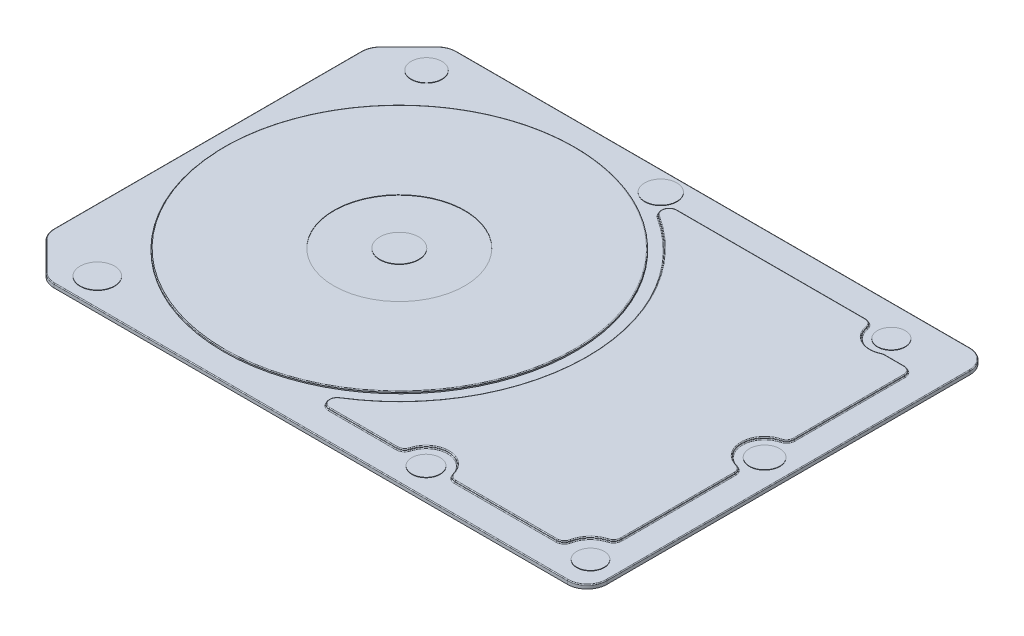
SolidWorks part; units mm, degrees
ref_plane "Front Plane" through (0, 0, 0) normal (0, 0, 1) x (1, 0, 0)
ref_plane "Top Plane" through (0, 0, 0) normal (0, 1, 0) x (1, 0, 0)
ref_plane "Right Plane" through (0, 0, 0) normal (1, 0, 0) x (0, 0, -1)
sketch "Sketch1" plane through (0, 0, 0) normal (0, 1, 0) x (1, 0, 0)
  line L0 (-72.0305, 42.3895) -> (-64.9595, 49.4605)
  line L1 (-61.4239, -50.925) -> (68.495, -50.925)
  line L2 (-73.495, -38.8539) -> (-73.495, 38.8539)
  line L3 (-61.4239, 50.925) -> (68.495, 50.925)
  line L4 (73.495, -45.925) -> (73.495, 45.925)
  line L5 (-73.495, -50.925) -> (73.495, 50.925) construction
  line L6 (-73.495, 50.925) -> (73.495, -50.925) construction
  line L7 (-72.0305, -42.3895) -> (-64.9595, -49.4605)
  arc A0 (-64.9595, -49.4605) -> (-61.4239, -50.925) centre (-61.4239, -45.925) ccw
  arc A1 (-72.0305, -42.3895) -> (-73.495, -38.8539) centre (-68.495, -38.8539) cw
  arc A2 (-72.0305, 42.3895) -> (-73.495, 38.8539) centre (-68.495, 38.8539) ccw
  arc A3 (-64.9595, 49.4605) -> (-61.4239, 50.925) centre (-61.4239, 45.925) cw
  arc A4 (68.495, -50.925) -> (73.495, -45.925) centre (68.495, -45.925) ccw
  arc A5 (68.495, 50.925) -> (73.495, 45.925) centre (68.495, 45.925) cw
  point P0 (0, 0)
  point P12 (-63.495, -50.925)
  point P15 (-73.495, -40.925)
  point P18 (-73.495, 40.925)
  point P21 (-63.495, 50.925)
  dimension "D3" = 5
  dimension "D1" = 146.99
  dimension "D2" = 101.85
extrude "cover base" add sketch "Sketch1" along normal blind 1
fillet "Fillet1" radius 0.2 12 edges at (-68.495, 1, 45.925) (-73.1144, 1, 40.7673) (-73.495, 1, 0) (-73.1144, 1, -40.7673) (-68.495, 1, -45.925) (-63.3373, 1, -50.5444) (3.5355, 1, -50.925) (72.0305, 1, -49.4605) (73.495, 1, 0) (72.0305, 1, 49.4605) (3.5355, 1, 50.925) (-63.3373, 1, 50.5444)
sketch "Sketch2" plane through (0, 1, 0) normal (0, 1, 0) x (1, 0, 0)
  circle A0 centre (-25, 0) radius 44.45
  dimension "D1" = 88.9
  dimension "D2" = 25
extrude "disk bulb" add sketch "Sketch2" along normal blind 0.5
fillet "Fillet2" radius 0.2 1 edges at (-25, 1.5, 44.45)
sketch "Sketch3" plane through (0, 1, 0) normal (0, 1, 0) x (1, 0, 0)
  line L0 (1.2049, -43.9217) -> (18.317, -43.9217)
  line L1 (33.0626, -43.9217) -> (58.7331, -43.9217)
  line L2 (66.696, -35.4916) -> (66.696, -6.7511)
  line L3 (66.696, 8.2828) -> (66.696, 36.1518)
  line L4 (64.696, 38.1518) -> (59.7928, 38.1518)
  line L5 (1.7404, 43.5821) -> (49.4372, 43.5821)
  arc A0 (0.6587, 39.8999) -> (0.1448, -40.2258) centre (-25, 0) cw
  arc A1 (51.4077, 41.9243) -> (58.9537, 37.9673) centre (56.7002, 42.8434) ccw
  arc A2 (65.2102, 6.35) -> (65.2102, -4.8184) centre (66.696, 0.7658) ccw
  arc A3 (60.6926, -42.3223) -> (65.243, -37.4153) centre (67.005, -43.6127) cw
  arc A4 (20.2473, -42.4453) -> (31.1323, -42.4453) centre (25.6898, -43.9217) cw
  arc A5 (49.4372, 43.5821) -> (51.4077, 41.9243) centre (49.4372, 41.5821) cw
  arc A6 (59.7928, 38.1518) -> (58.9537, 37.9673) centre (59.7928, 36.1518) ccw
  arc A7 (66.696, 36.1518) -> (64.696, 38.1518) centre (64.696, 36.1518) ccw
  arc A8 (66.696, 8.2828) -> (65.2102, 6.35) centre (64.696, 8.2828) cw
  arc A9 (66.696, -6.7511) -> (65.2102, -4.8184) centre (64.696, -6.7511) ccw
  arc A10 (66.696, -35.4916) -> (65.243, -37.4153) centre (64.696, -35.4916) cw
  arc A11 (58.7331, -43.9217) -> (60.6926, -42.3223) centre (58.7331, -41.9217) ccw
  arc A12 (33.0626, -43.9217) -> (31.1323, -42.4453) centre (33.0626, -41.9217) cw
  arc A13 (18.317, -43.9217) -> (20.2473, -42.4453) centre (18.317, -41.9217) ccw
  arc A14 (0.1448, -40.2258) -> (1.2049, -43.9217) centre (1.2049, -41.9217) ccw
  arc A15 (0.6587, 39.8999) -> (1.7404, 43.5821) centre (1.7404, 41.5821) cw
  point P0 (-25, 0)
  point P28 (66.696, -5.0126)
  point P37 (20.0506, -43.9217)
  dimension "D1" = 2
extrude "hardware bulging" add sketch "Sketch3" along normal blind 0.5
fillet "Fillet3" radius 0.2 22 edges at (54.2055, 1.5, -38.0861) (59.3632, 1.5, -38.1051) (62.2444, 1.5, -38.1518) (66.1102, 1.5, -37.566) (66.696, 1.5, -22.2173) (66.2816, 1.5, -7.0638) (60.9175, 1.5, -0.7658) (66.2816, 1.5, 5.5322) (66.696, 1.5, 21.1213) (66.2919, 1.5, 36.697) (62.2807, 1.5, 39.2317) (59.9978, 1.5, 43.4711) (45.8978, 1.5, 43.9217) (31.8475, 1.5, 43.5103) (25.6898, 1.5, 38.2825) (19.5321, 1.5, 43.5103) (9.761, 1.5, 43.9217) (-0.7176, 1.5, 42.4731) (22.4371, 1.5, 0.3042) (-0.1785, 1.5, -42.1459) (25.5888, 1.5, -43.5821) (50.7248, 1.5, -43.1126)
fillet "Fillet4" radius 0.2 22 edges at (19.5321, 1, 43.5103) (9.761, 1, 43.9217) (-0.7176, 1, 42.4731) (22.4371, 1, 0.3042) (-0.1785, 1, -42.1459) (25.5888, 1, -43.5821) (50.7248, 1, -43.1126) (54.2055, 1, -38.0861) (59.3632, 1, -38.1051) (62.2444, 1, -38.1518) (66.1102, 1, -37.566) (66.696, 1, -22.2173) (66.2816, 1, -7.0638) (60.9175, 1, -0.7658) (66.2816, 1, 5.5322) (66.696, 1, 21.1213) (66.2919, 1, 36.697) (62.2807, 1, 39.2317) (59.9978, 1, 43.4711) (45.8978, 1, 43.9217) (31.8475, 1, 43.5103) (25.6898, 1, 38.2825)
sketch "Sketch4" plane through (0, 1, 0) normal (0, 1, 0) x (1, 0, 0)
  circle A0 centre (56.7002, 42.8434) radius 3.5111
  circle A1 centre (66.696, 0.7658) radius 3.8342
  circle A2 centre (67.005, -43.6127) radius 3.4719
  circle A3 centre (25.6898, -43.9217) radius 3.5853
  circle A4 centre (-57.5061, -43.9217) radius 4.3531
  circle A5 centre (-60.9566, 42.8434) radius 3.8953
  circle A6 centre (-4.5851, 45.7711) radius 4.0669
extrude "screw caps" add sketch "Sketch4" along normal blind 0.1
sketch "Sketch5" plane through (0, 1.5, 0) normal (0, 1, 0) x (1, 0, 0)
  circle A0 centre (-25, 0) radius 4.9251
  circle A1 centre (-25, 0) radius 16.567
extrude "Cut-Extrude1" cut sketch "Sketch5" against normal blind 0.1
